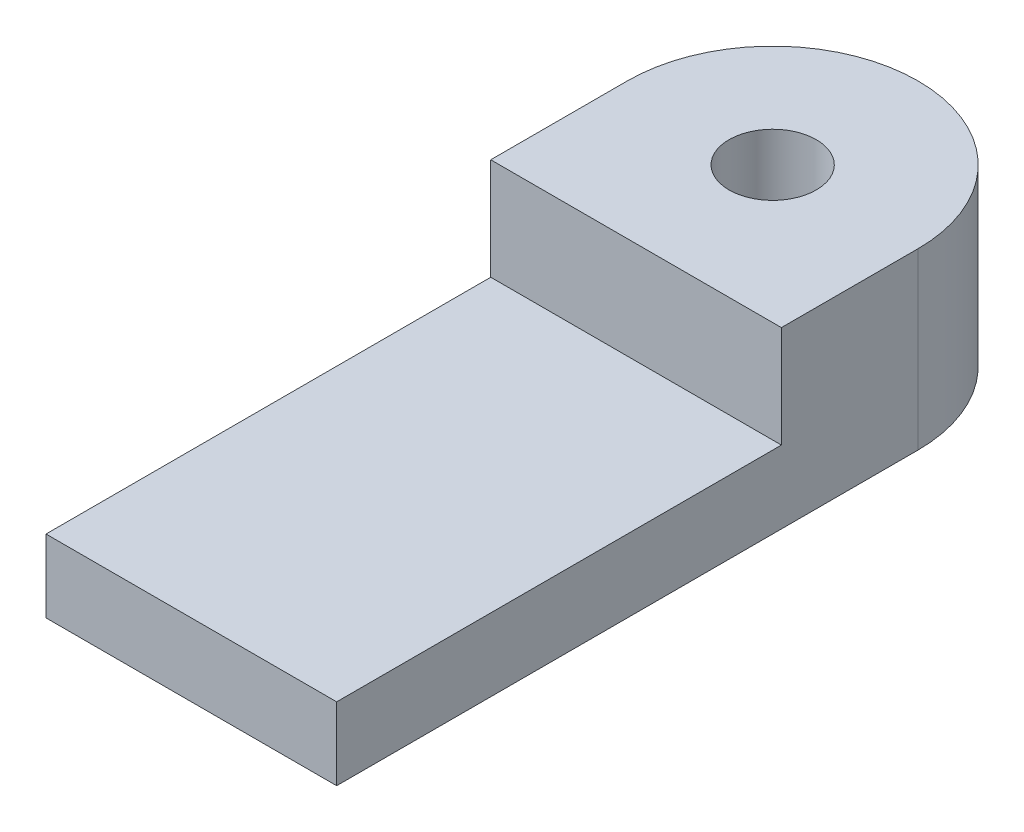
SolidWorks part; units mm, degrees
ref_plane "Ebene vorne" through (0, 0, 0) normal (0, 0, 1) x (1, 0, 0)
ref_plane "Ebene oben" through (0, 0, 0) normal (0, 1, 0) x (1, 0, 0)
ref_plane "Ebene rechts" through (0, 0, 0) normal (1, 0, 0) x (0, 0, -1)
sketch "Skizze1" plane through (0, 0, 0) normal (0, 1, 0) x (1, 0, 0)
  line L0 (0, 0) -> (0, 20)
  line L1 (10, 20) -> (10, 0)
  line L2 (10, 0) -> (0, 0)
  arc A0 (0, 20) -> (10, 20) centre (5, 20) cw
  dimension "D2" = 5
  dimension "D1" = 20
extrude "Aufsatz-Linear austragen1" add sketch "Skizze1" along normal blind 2.5
sketch "Skizze2" plane through (0, 2.5, 0) normal (0, 1, 0) x (1, 0, 0)
  line L0 (0, 20) -> (0, 15.3)
  line L1 (0, 20) -> (0, 0) construction
  line L2 (0, 15.3) -> (10, 15.3)
  line L3 (10, 0) -> (10, 20) construction
  line L4 (10, 15.3) -> (10, 20)
  line L5 (0, 0) -> (10, 0) construction
  arc A0 (10, 20) -> (0, 20) centre (5, 20) ccw
  dimension "D1" = 15.3
extrude "Aufsatz-Linear austragen2" add sketch "Skizze2" along normal blind 3.5
sketch "Skizze3" plane through (0, 6, 0) normal (0, 1, 0) x (1, 0, 0)
  line L0 (0, 20) -> (10, 20) construction
  circle A0 centre (5, 20) radius 1.5
  point P6 (0, 0)
  point P7 (10, 17)
  dimension "D1" = 3
extrude "Schnitt-Linear austragen1" cut sketch "Skizze3" against normal through all
